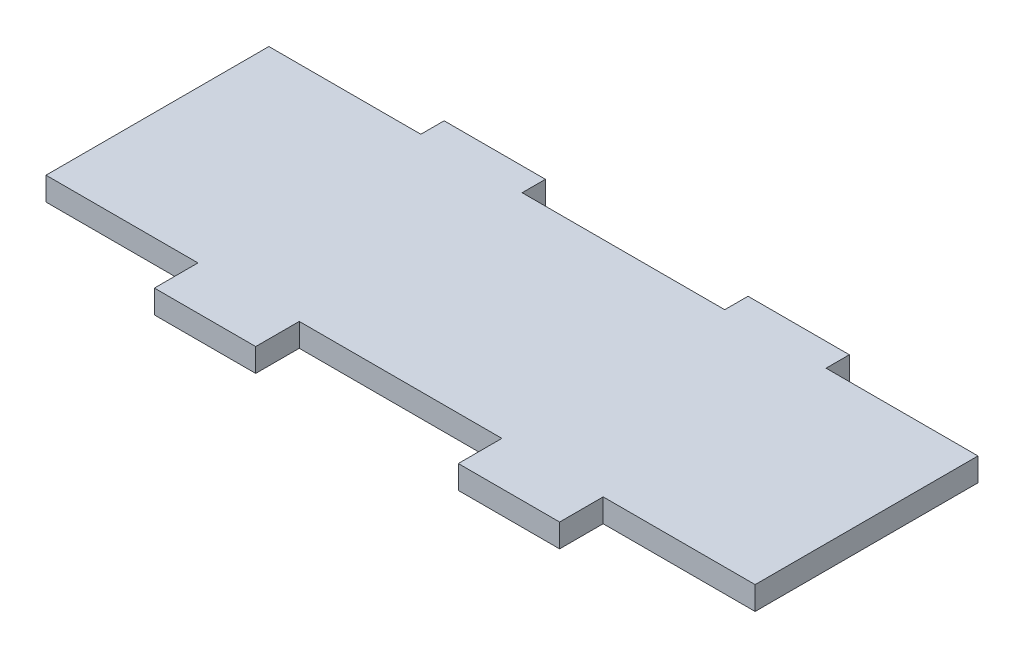
SolidWorks part; units mm, degrees
ref_plane "Front Plane" through (0, 0, 0) normal (0, 0, 1) x (1, 0, 0)
ref_plane "Top Plane" through (0, 0, 0) normal (0, 1, 0) x (1, 0, 0)
ref_plane "Right Plane" through (0, 0, 0) normal (1, 0, 0) x (0, 0, -1)
sketch "Sketch1" plane through (0, 0, 0) normal (0, 1, 0) x (1, 0, 0)
  line L0 (0, 0) -> (70, 0) construction
  line L1 (0, 0) -> (0, 22)
  line L2 (0, -4.3) -> (70, -4.3) construction
  line L3 (0, 0) -> (0, -4.3) construction
  line L4 (0, 22) -> (0, 24.3) construction
  line L5 (0, 22) -> (70, 22) construction
  line L6 (70, 22) -> (70, 0)
  line L7 (0, 24.3) -> (70, 24.3) construction
  line L8 (70, 24.3) -> (70, 22) construction
  line L9 (70, -4.3) -> (70, 0) construction
  line L10 (35, -4.3) -> (25, -4.3) construction
  line L11 (35, -4.3) -> (45, -4.3) construction
  line L12 (25, -4.3) -> (15, -4.3) construction
  line L13 (45, -4.3) -> (55, -4.3) construction
  line L14 (15, -4.3) -> (15, 24.3) construction
  line L15 (25, -4.3) -> (25, 24.3) construction
  line L16 (45, -4.3) -> (45, 24.3) construction
  line L17 (55, -4.3) -> (55, 24.3) construction
  line L18 (0, 22) -> (15, 22)
  line L19 (15, 22) -> (15, 24.3)
  line L20 (15, 24.3) -> (25, 24.3)
  line L21 (25, 24.3) -> (25, 22)
  line L22 (25, 22) -> (45, 22)
  line L23 (45, 22) -> (45, 24.3)
  line L24 (45, 24.3) -> (55, 24.3)
  line L25 (55, 24.3) -> (55, 22)
  line L26 (55, 22) -> (70, 22)
  line L27 (0, 0) -> (15, 0)
  line L28 (15, 0) -> (15, -4.3)
  line L29 (15, -4.3) -> (25, -4.3)
  line L30 (25, -4.3) -> (25, 0)
  line L31 (25, 0) -> (45, 0)
  line L32 (45, 0) -> (45, -4.3)
  line L33 (45, -4.3) -> (55, -4.3)
  line L34 (55, -4.3) -> (55, 0)
  line L35 (55, 0) -> (70, 0)
  dimension "D1" = 70
  dimension "D2" = 22
  dimension "D3" = 10
  dimension "D4" = 4.3
  dimension "D5" = 2.3
  dimension "D6" = 10
  dimension "D7" = 10
  dimension "D8" = 10
extrude "Boss-Extrude1" add sketch "Sketch1" along normal blind 2.3
